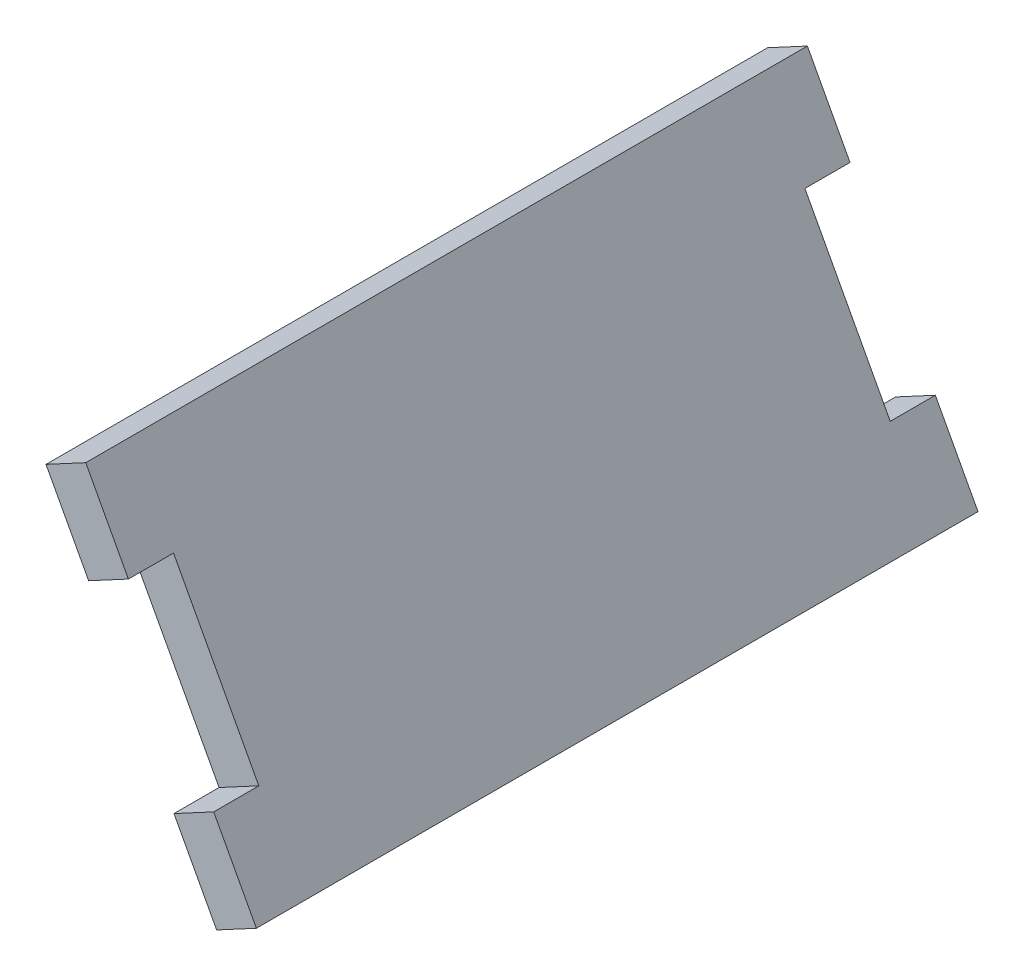
SolidWorks part; units mm, degrees
ref_plane "Front Plane" through (0, 0, 0) normal (0, 0, 1) x (1, 0, 0)
ref_plane "Top Plane" through (0, 0, 0) normal (0, 1, 0) x (1, 0, 0)
ref_plane "Right Plane" through (0, 0, 0) normal (1, 0, 0) x (0, 0, -1)
sketch "Sketch1" plane through (0, 0, 0) normal (0, 0, 1) x (1, 0, 0)
  line L0 (149.5088, 324.2522) -> (161.5202, 301.8718)
  line L1 (161.5202, 301.8718) -> (158.7227, 300.3703)
  line L2 (158.7227, 300.3703) -> (146.7112, 322.7508)
  line L3 (146.7112, 322.7508) -> (149.5088, 324.2522)
  dimension "D1" = 3.175
  dimension "D2" = 25.4
extrude "Boss-Extrude1" add sketch "Sketch1" against normal up to vertex (50.8 mm away) contours L0 L1 L2 L3
sketch "Sketch2" plane through (251.1823, 134.8082, 0) normal (0.8811, 0.4729, 0) x (0, 0, -1)
  line L0 (0, 215.0036) -> (0, 189.6036) construction
  line L1 (0, 208.6536) -> (3.175, 208.6536)
  line L2 (0, 208.6536) -> (0, 195.9536)
  line L3 (0, 195.9536) -> (3.175, 195.9536)
  line L4 (3.175, 208.6536) -> (3.175, 195.9536)
  line L5 (3.175, 184.3349) -> (3.175, 242.1644) construction
  line L6 (47.625, 242.1644) -> (47.625, 184.3349) construction
  line L7 (47.625, 195.9536) -> (50.8, 195.9536)
  line L8 (47.625, 195.9536) -> (47.625, 208.6536)
  line L9 (47.625, 208.6536) -> (50.8, 208.6536)
  line L10 (50.8, 195.9536) -> (50.8, 208.6536)
  line L11 (50.8, 215.0036) -> (50.8, 189.6036) construction
  line L12 (50.8, 215.0036) -> (0, 215.0036) construction
  line L13 (50.8, 189.6036) -> (0, 189.6036) construction
  dimension "D1" = 6.35
  dimension "D2" = 6.35
  dimension "D3" = 6.35
  dimension "D4" = 6.35
extrude "Cut-Extrude1" cut sketch "Sketch2" against normal blind 3.175
